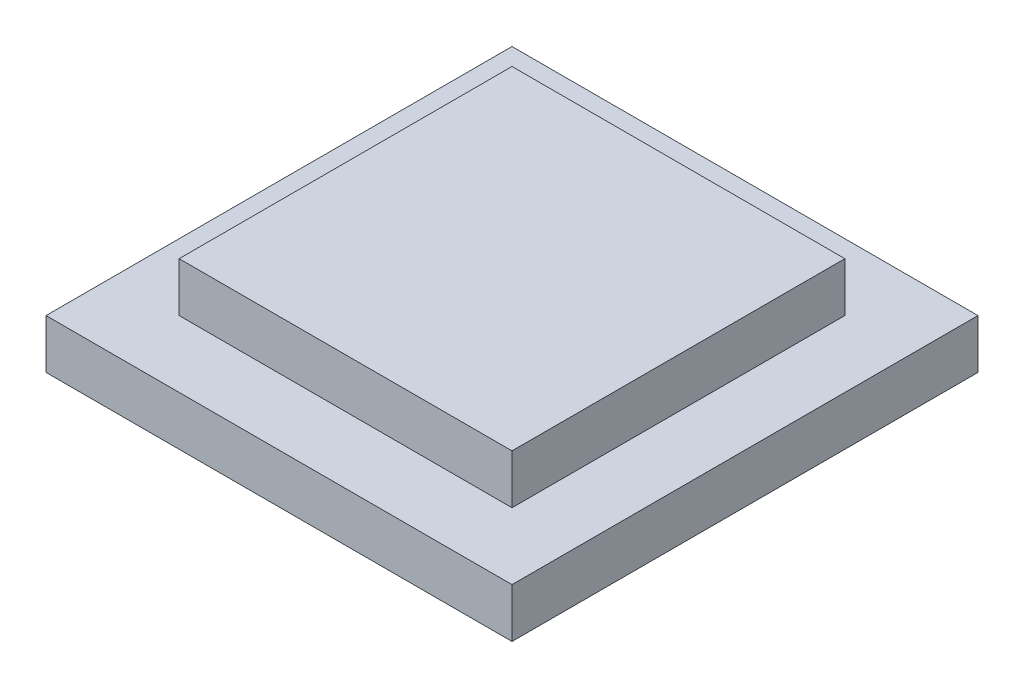
SolidWorks part; units mm, degrees
ref_plane "Front Plane" through (0, 0, 0) normal (0, 0, 1) x (1, 0, 0)
ref_plane "Top Plane" through (0, 0, 0) normal (0, 1, 0) x (1, 0, 0)
ref_plane "Right Plane" through (0, 0, 0) normal (1, 0, 0) x (0, 0, -1)
sketch "Sketch1" plane through (0, 0, 0) normal (0, 1, 0) x (1, 0, 0)
  line L1 (-17.5, -17.5) -> (17.5, -17.5)
  line L2 (-17.5, -17.5) -> (-17.5, 17.5)
  line L3 (-17.5, 17.5) -> (17.5, 17.5)
  line L4 (17.5, -17.5) -> (17.5, 17.5)
  line L5 (-17.5, -17.5) -> (17.5, 17.5) construction
  line L6 (-17.5, 17.5) -> (17.5, -17.5) construction
  point P0 (0, 0)
  dimension "D1" = 35
extrude "Boss-Extrude1" add sketch "Sketch1" along normal blind 3.7
sketch "Sketch2" plane through (0, 3.7, 0) normal (0, 1, 0) x (1, 0, 0)
  line L1 (-12.5, -12.5) -> (12.5, -12.5)
  line L2 (-12.5, -12.5) -> (-12.5, 12.5)
  line L3 (-12.5, 12.5) -> (12.5, 12.5)
  line L4 (12.5, -12.5) -> (12.5, 12.5)
  line L5 (-12.5, -12.5) -> (12.5, 12.5) construction
  line L6 (-12.5, 12.5) -> (12.5, -12.5) construction
  point P0 (0, 0)
  dimension "D1" = 25
extrude "Boss-Extrude2" add sketch "Sketch2" along normal blind 3.7
equation "\"D1@Boss-Extrude2\"=11.1/3"
equation "\"D1@Boss-Extrude1\"=11.1/3"
